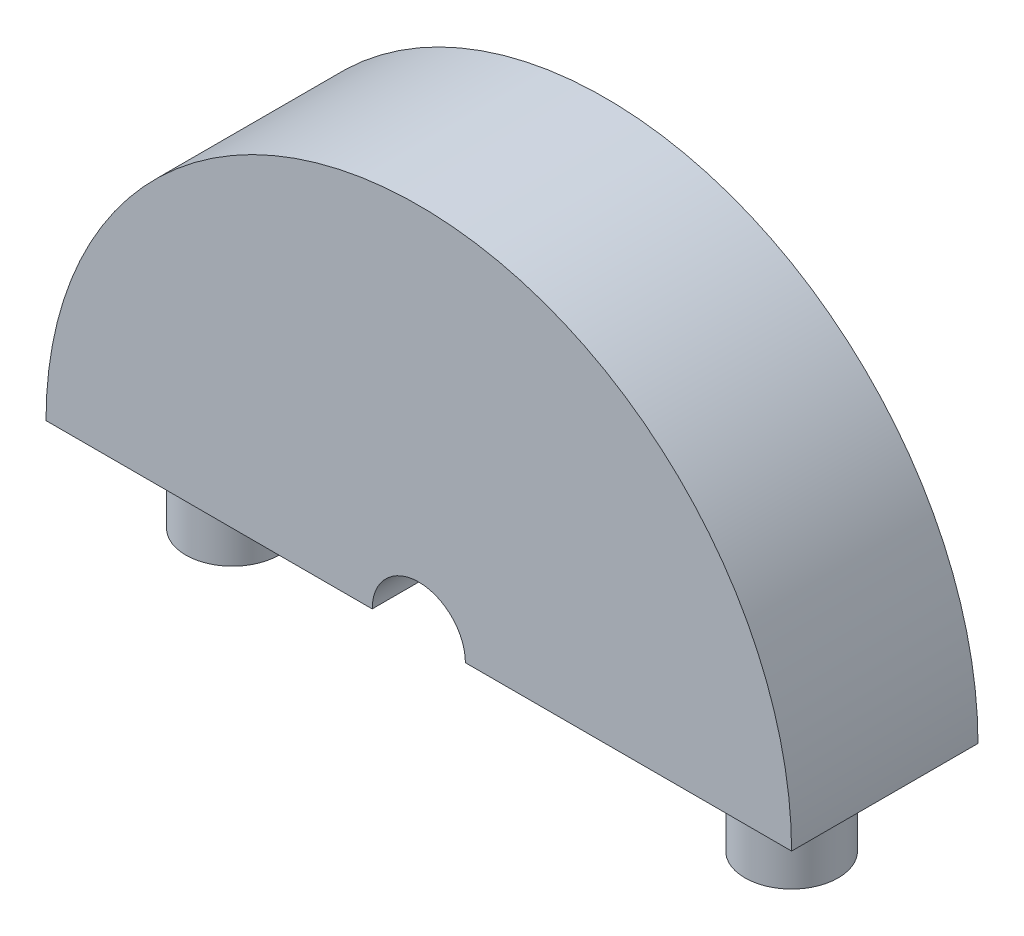
SolidWorks part; units mm, degrees
ref_plane "Front Plane" through (0, 0, 0) normal (0, 0, 1) x (1, 0, 0)
ref_plane "Top Plane" through (0, 0, 0) normal (0, 1, 0) x (1, 0, 0)
ref_plane "Right Plane" through (0, 0, 0) normal (1, 0, 0) x (0, 0, -1)
sketch "Sketch2" plane through (0, 0, 0) normal (0, 0, 1) x (1, 0, 0)
  line L0 (20, 0) -> (-20, 0)
  arc A0 (20, 0) -> (-20, 0) centre (0, 0) ccw
  dimension "D1" = 40
extrude "Boss-Extrude1" add sketch "Sketch2" along normal blind 10
sketch "Sketch4" plane through (0, 0, 0) normal (1, 0, 0) x (0, 0, -1)
  line L0 (-17.1339, 0) -> (2.3849, 0) construction
  line L1 (-10, 0) -> (-10, 2.5)
  line L2 (-10, 20) -> (-10, 0) construction
  line L3 (-10, 2.5) -> (0, 2.5)
  line L9 (0, 2.5) -> (0, 0)
  line L10 (0, 0) -> (-10, 0)
  dimension "D1" = 2.5
  dimension "D3" = 10
revolve "Cut-Revolve1" cut sketch "Sketch4" angle 360 about L0
sketch "Sketch5" plane through (0, 0, 0) normal (0, -1, 0) x (1, 0, 0)
  line L0 (-20, 10) -> (-2.5, 10) construction
  line L1 (-20, 10) -> (-20, 0) construction
  line L2 (20, 10) -> (20, 0) construction
  circle A0 centre (-15, 5) radius 2.5
  circle A1 centre (15, 5) radius 2.5
  dimension "D4" = 5
  dimension "D1" = 5
  dimension "D2" = 5
  dimension "D3" = 5
extrude "Boss-Extrude2" add sketch "Sketch5" along normal blind 5
